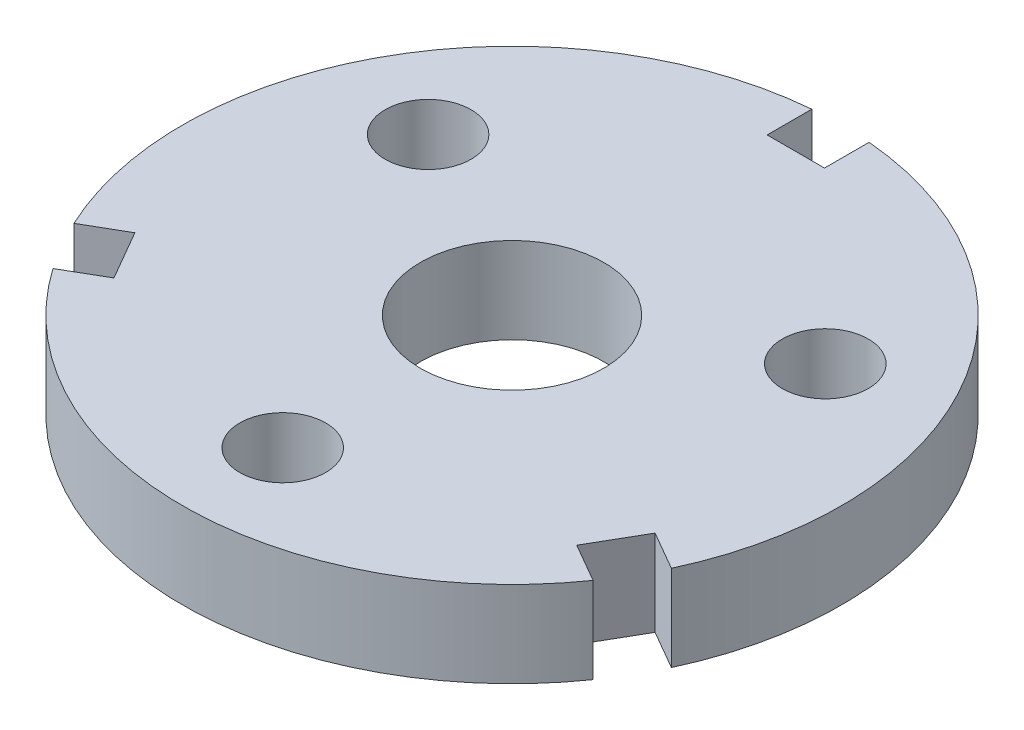
SolidWorks part; units mm, degrees
ref_plane "Front Plane" through (0, 0, 0) normal (0, 0, 1) x (1, 0, 0)
ref_plane "Top Plane" through (0, 0, 0) normal (0, 1, 0) x (1, 0, 0)
ref_plane "Right Plane" through (0, 0, 0) normal (1, 0, 0) x (0, 0, -1)
sketch "Sketch1" plane through (0, 0, 0) normal (0, 1, 0) x (1, 0, 0)
  line L0 (52.1078, -24.311) -> (45.3683, -20.4199)
  line L2 (-5, 57.2822) -> (-5, 49.5)
  line L3 (-5, 49.5) -> (5, 49.5)
  line L4 (5, 57.2822) -> (5, 49.5)
  line L5 (0, 0) -> (32.9228, 0) construction
  line L6 (34.641, 20) -> (0, 0) construction
  line L7 (45.3683, -20.4199) -> (40.3683, -29.0801)
  line L8 (47.1078, -32.9712) -> (40.3683, -29.0801)
  line L9 (-47.1078, -32.9712) -> (-40.3683, -29.0801)
  line L10 (-40.3683, -29.0801) -> (-45.3683, -20.4199)
  line L11 (-52.1078, -24.311) -> (-45.3683, -20.4199)
  arc A0 (-5, 57.2822) -> (-52.1078, -24.311) centre (0, 0) ccw
  circle A1 centre (0, 0) radius 40 construction
  circle A2 centre (0, 0) radius 16
  circle A3 centre (0, -40) radius 7.5
  circle A4 centre (-34.641, 20) radius 7.5
  circle A5 centre (34.641, 20) radius 7.5
  arc A6 (52.1078, -24.311) -> (5, 57.2822) centre (0, 0) ccw
  arc A7 (-47.1078, -32.9712) -> (47.1078, -32.9712) centre (0, 0) ccw
  point P7 (0, 57.5)
  point P28 (0, 0)
  dimension "D1" = 80
  dimension "D2" = 32
  dimension "D3" = 115
  dimension "D4" = 15
  dimension "D5" = 8
  dimension "D6" = 3
  dimension "D7" = 30
extrude "Boss-Extrude1" add sketch "Sketch1" along normal mid plane 15
